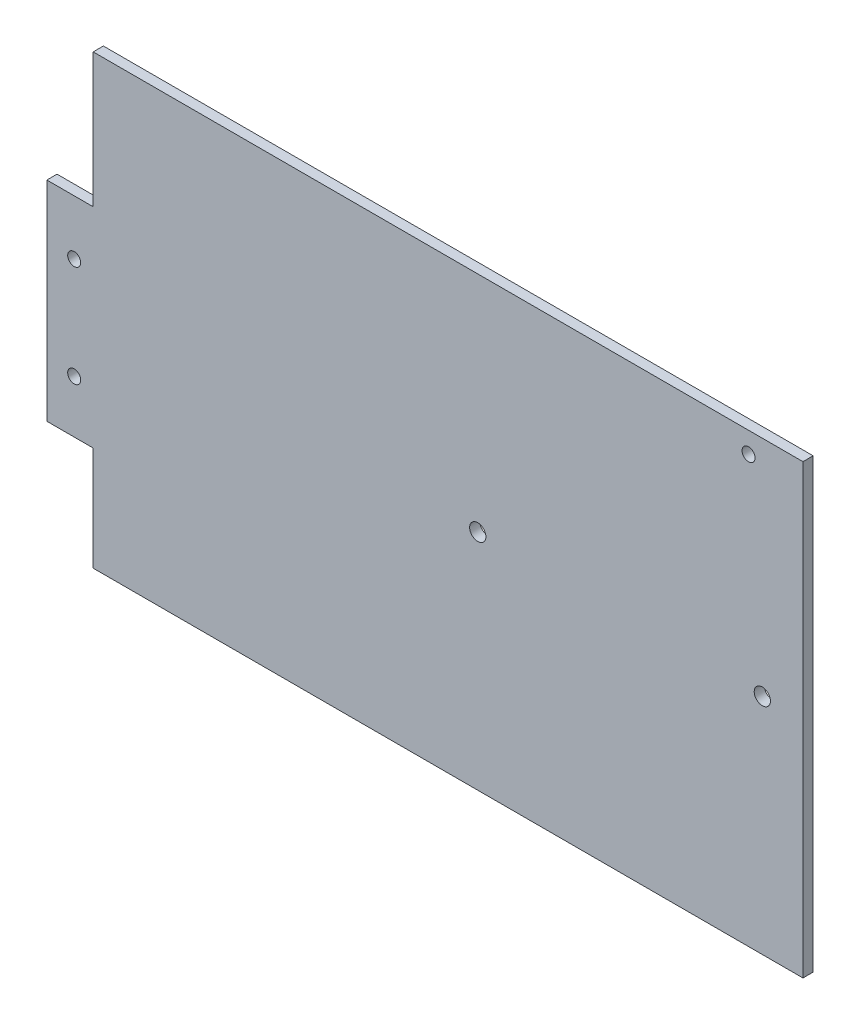
SolidWorks part; units mm, degrees
ref_plane "Front Plane" through (0, 0, 0) normal (0, 0, 1) x (1, 0, 0)
ref_plane "Top Plane" through (0, 0, 0) normal (0, 1, 0) x (1, 0, 0)
ref_plane "Right Plane" through (0, 0, 0) normal (1, 0, 0) x (0, 0, -1)
sketch "Sketch1" plane through (0, 0, 0) normal (0, 0, 1) x (1, 0, 0)
  line L0 (-221.742, 69.85) -> (0, 69.85) construction
  line L1 (0, 0) -> (-221.742, 0)
  line L2 (0, 0) -> (0, 139.7)
  line L3 (0, 139.7) -> (-221.742, 139.7)
  line L4 (-221.742, 0) -> (-221.742, 139.7)
  line L5 (-110.871, 139.7) -> (-110.871, 0) construction
  line L6 (-221.742, 97.79) -> (-236.22, 97.79)
  line L7 (-221.742, 32.512) -> (-236.22, 32.512)
  line L8 (-236.22, 97.79) -> (-236.22, 32.512)
  line L9 (-303.3951, 65.151) -> (-302.9884, 65.151)
  dimension "D1" = 139.7
  dimension "D2" = 221.742
  dimension "D3" = 41.91
  dimension "D4" = 32.512
  dimension "D5" = 14.478
extrude "Boss-Extrude3" add sketch "Sketch1" along normal blind 3.175 contours L4 L1 L2 L3 | L6 L8 L7 L4
sketch "Sketch3" plane through (0, 0, 0) normal (0, 0, -1) x (-1, 0, 0)
  circle A0 centre (227.6801, 80.6813) radius 2.032
  circle A1 centre (227.6801, 48.9313) radius 2.032
  dimension "D1" = 4.064
  dimension "D2" = 4.064
extrude "Cut-Extrude2" cut sketch "Sketch3" against normal through all
sketch "Sketch4" plane through (0, 0, 3.175) normal (0, 0, 1) x (1, 0, 0)
  line L0 (0, 0) -> (0, 139.7) construction
  line L1 (0, 139.7) -> (-221.742, 139.7) construction
  circle A0 centre (-17, 133.2) radius 2.032
  dimension "D1" = 4.064
  dimension "D2" = 17
  dimension "D3" = 6.5
extrude "Cut-Extrude3" cut sketch "Sketch4" against normal through all
sketch "Sketch5" plane through (0, 0, 3.175) normal (0, 0, 1) x (1, 0, 0)
  line L0 (0, 0) -> (0, 139.7) construction
  line L1 (0, 0) -> (-221.742, 0) construction
  circle A0 centre (-101.6, 69.85) radius 2.54
  circle A1 centre (-12.7, 69.85) radius 2.54
  dimension "D2" = 5.08
  dimension "D3" = 5.08
  dimension "D1" = 88.9
  dimension "D4" = 12.7
  dimension "D5" = 69.85
extrude "Cut-Extrude4" cut sketch "Sketch5" against normal through all
